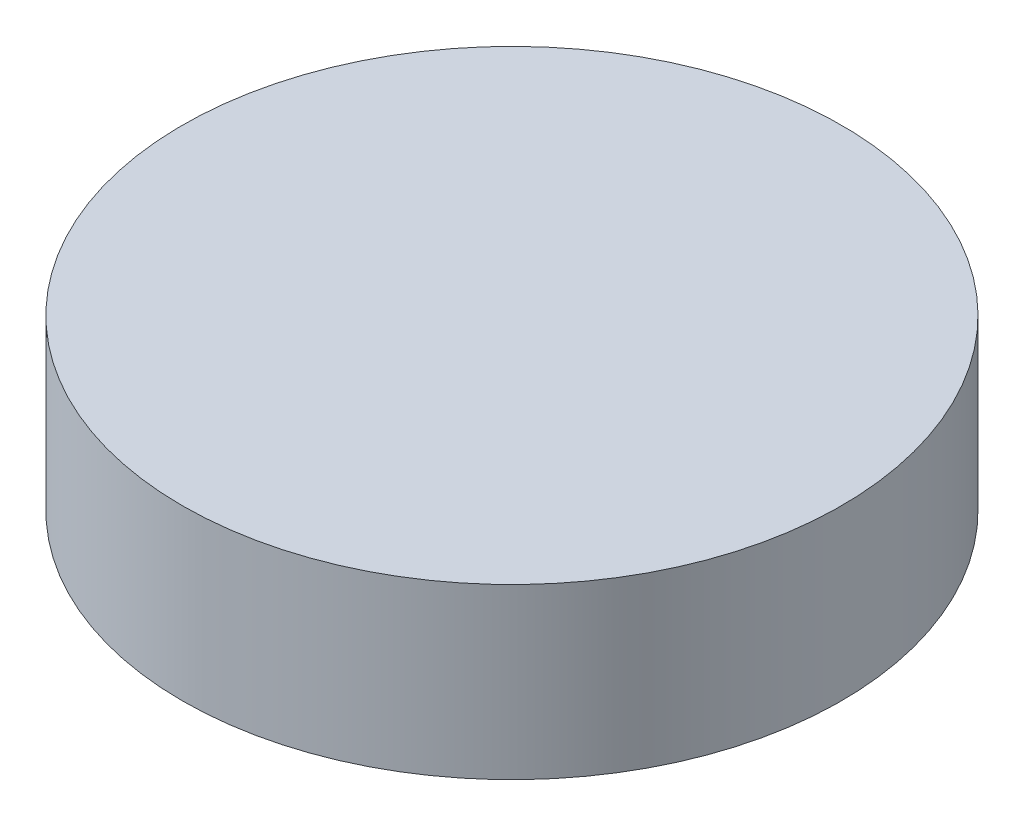
SolidWorks part; units mm, degrees
ref_plane "Front Plane" through (0, 0, 0) normal (0, 0, 1) x (1, 0, 0)
ref_plane "Top Plane" through (0, 0, 0) normal (0, 1, 0) x (1, 0, 0)
ref_plane "Right Plane" through (0, 0, 0) normal (1, 0, 0) x (0, 0, -1)
sketch "Sketch1" plane through (0, 0, 0) normal (0, 1, 0) x (1, 0, 0)
  circle A0 centre (0, 0) radius 19.5
  dimension "D1" = 39
extrude "Boss-Extrude1" add sketch "Sketch1" along normal blind 10
